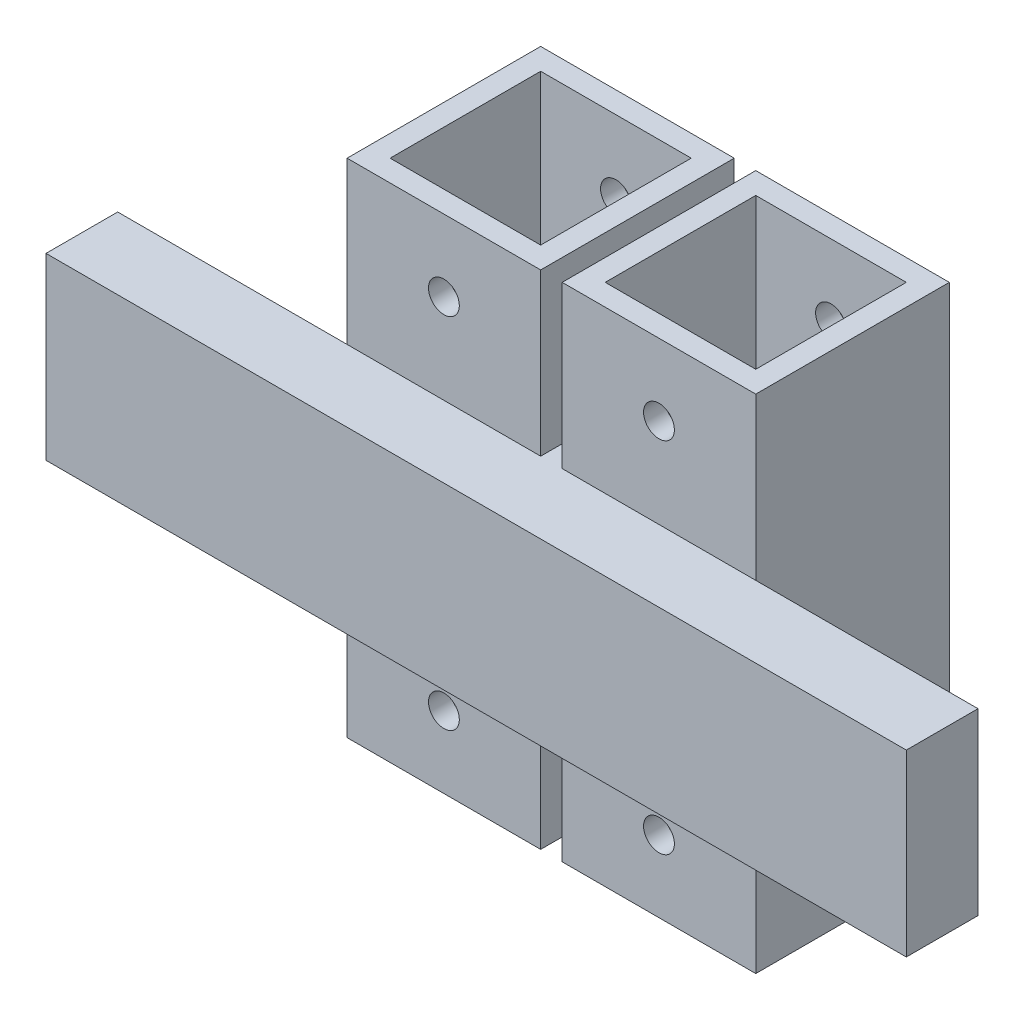
SolidWorks part; units mm, degrees
ref_plane "Front Plane" through (0, 0, 0) normal (0, 0, 1) x (1, 0, 0)
ref_plane "Top Plane" through (0, 0, 0) normal (0, 1, 0) x (1, 0, 0)
ref_plane "Right Plane" through (0, 0, 0) normal (1, 0, 0) x (0, 0, -1)
sketch "Sketch1" plane through (0, 0, 0) normal (0, 1, 0) x (1, 0, 0)
  line L1 (0, 0) -> (27, 0)
  line L2 (0, 0) -> (0, 27)
  line L3 (0, 27) -> (27, 27)
  line L4 (27, 0) -> (27, 27)
  line L5 (3, 24) -> (24, 24)
  line L6 (3, 24) -> (3, 3)
  line L7 (3, 3) -> (24, 3)
  line L8 (24, 24) -> (24, 3)
  line L9 (-30, 27) -> (-3, 27)
  line L10 (-30, 27) -> (-30, 0)
  line L11 (-30, 0) -> (-3, 0)
  line L12 (-3, 27) -> (-3, 0)
  line L13 (-6, 24) -> (-27, 24)
  line L14 (-6, 24) -> (-6, 3)
  line L15 (-6, 3) -> (-27, 3)
  line L16 (-27, 24) -> (-27, 3)
  line L17 (-26.5, 23.5) -> (-6.5, 23.5) construction
  line L18 (-26.5, 23.5) -> (-26.5, 3.5) construction
  line L19 (-26.5, 3.5) -> (-6.5, 3.5) construction
  line L20 (-6.5, 23.5) -> (-6.5, 3.5) construction
  line L21 (3.5, 23.5) -> (23.5, 23.5) construction
  line L22 (3.5, 23.5) -> (3.5, 3.5) construction
  line L23 (3.5, 3.5) -> (23.5, 3.5) construction
  line L24 (23.5, 23.5) -> (23.5, 3.5) construction
  dimension "D1" = 10
  dimension "D2" = 0.5
  dimension "D3" = 3
  dimension "D4" = 3
  dimension "D5" = 3
  dimension "D6" = 3
  dimension "D7" = 3
  dimension "D8" = 20
  dimension "D9" = 0.5
  dimension "D10" = 0.5
  dimension "D11" = 0.5
extrude "Boss-Extrude1" add sketch "Sketch1" along normal blind 70
sketch "Sketch2" plane through (0, 0, 0) normal (0, 0, 1) x (1, 0, 0)
  line L0 (-30, 70) -> (-30, 0) construction
  line L1 (-62, 47.5) -> (58, 47.5)
  line L2 (-62, 47.5) -> (-62, 22.5)
  line L3 (-62, 22.5) -> (58, 22.5)
  line L4 (58, 47.5) -> (58, 22.5)
  line L5 (-52, 42.5) -> (48, 42.5) construction
  line L6 (-52, 42.5) -> (-52, 27.5) construction
  line L7 (-52, 27.5) -> (48, 27.5) construction
  line L8 (48, 42.5) -> (48, 27.5) construction
  point P8 (-2, 27.5)
  point P9 (-2, 22.5)
  point P10 (-62, 35)
  point P11 (-52, 35)
  point P14 (-30, 35)
  dimension "D1" = 100
  dimension "D2" = 10
  dimension "D3" = 22
  dimension "D4" = 25
  dimension "D5" = 5
extrude "Boss-Extrude2" add sketch "Sketch2" along normal blind 10
sketch "Sketch3" plane through (0, 0, -27) normal (0, 0, -1) x (-1, 0, 0)
  line L1 (0, 47.5) -> (3, 47.5)
  line L2 (0, 47.5) -> (0, 22.5)
  line L3 (0, 22.5) -> (3, 22.5)
  line L4 (3, 47.5) -> (3, 22.5)
extrude "Boss-Extrude3" add sketch "Sketch3" against normal up to surface (27 mm away) up to face at (42.5, 35, 0)
sketch "Sketch4" plane through (0, 0, -27) normal (0, 0, -1) x (-1, 0, 0)
  line L1 (-13.5, 60) -> (16.5, 60) construction
  line L2 (-13.5, 60) -> (-13.5, 10) construction
  line L3 (-13.5, 10) -> (16.5, 10) construction
  line L4 (16.5, 60) -> (16.5, 10) construction
  line L5 (-27, 0) -> (0, 0) construction
  line L7 (3, 0) -> (30, 0) construction
  circle A0 centre (-13.5, 60) radius 2.15
  circle A1 centre (16.5, 60) radius 2.15
  circle A2 centre (-13.5, 10) radius 2.15
  circle A3 centre (16.5, 10) radius 2.15
  point P13 (-13.5, 0)
  point P15 (16.5, 0)
  dimension "D1" = 4.3
  dimension "D2" = 50
  dimension "D3" = 10
extrude "Cut-Extrude1" cut sketch "Sketch4" against normal through all
